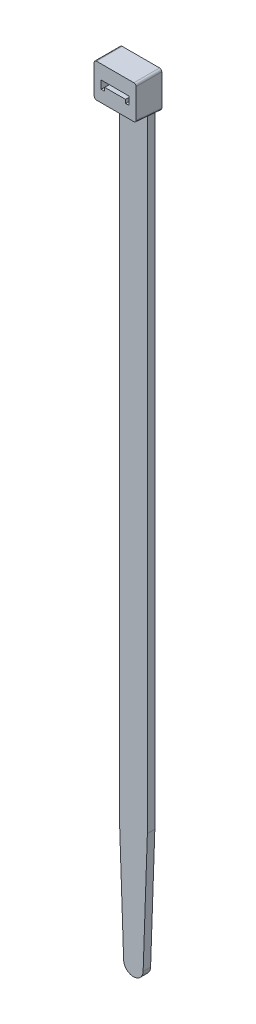
SolidWorks part; units mm, degrees
ref_plane "Front Plane" through (0, 0, 0) normal (0, 0, 1) x (1, 0, 0)
ref_plane "Top Plane" through (0, 0, 0) normal (0, 1, 0) x (1, 0, 0)
ref_plane "Right Plane" through (0, 0, 0) normal (1, 0, 0) x (0, 0, -1)
sketch "Sketch1" plane through (0, 0, 0) normal (0, 0, 1) x (1, 0, 0)
  line L0 (0, 0) -> (0, -49.9735) construction
  line L1 (-22.1748, 6.5086) -> (4.8438, 6.5086) construction
  line L2 (3.81, 0) -> (3.81, -180.234)
  line L3 (-3.81, -180.234) -> (-3.81, 7.4712) construction
  line L4 (3.81, -180.234) -> (2.654, -213.337)
  line L7 (3.81, 0) -> (0, 0)
  line L8 (0, -215.9) -> (0, 0)
  line L9 (0, -9.8) -> (6.4573, -9.8) construction
  arc A0 (2.654, -213.337) -> (0, -215.9) centre (0, -213.2444) cw
  dimension "D1" = 7.62
  dimension "D2" = 9.8
  dimension "D3" = 170.434
  dimension "D4" = 215.9
  dimension "D6" = 2
extrude "Boss-Extrude1" add sketch "Sketch1" along normal blind 2.032
sketch "Sketch5" plane through (0, 0, 0) normal (-1, 0, 0) x (0, 0, 1)
  line L0 (0, 0) -> (7, 0)
  line L1 (7, 0) -> (7, -9.1876)
  line L2 (7, -9.1876) -> (0, -9.8)
  line L4 (0, -9.8) -> (0, 0)
  dimension "D1" = 5
  dimension "D2" = 7
extrude "Boss-Extrude2" add sketch "Sketch5" against normal blind 5.7
sketch "Sketch4" plane through (0, 0, 7) normal (0, 0, 1) x (1, 0, 0)
  line L0 (0, -3.8) -> (3.8, -3.8)
  line L1 (0, -9.6222) -> (0, -215.9) construction
  line L2 (3.8, -3.8) -> (3.8, -6)
  line L3 (3.8, -6) -> (2.85, -6)
  line L4 (2.85, -6) -> (2.85, -5.05)
  line L5 (2.85, -5.05) -> (0, -5.05)
  line L6 (0, -5.05) -> (0, -3.8)
  line L8 (0, 0) -> (0, -9.0011) construction
  line L9 (5.7, 0) -> (0, 0) construction
  dimension "D1" = 3.8
  dimension "D2" = 7.6
  dimension "D3" = 2.2
  dimension "D4" = 1.25
  dimension "D5" = 5.7
extrude "Cut-Extrude1" cut sketch "Sketch4" against normal up to surface (7 mm away) up to face at (3.1703, -89.9439, 0)
fillet "Fillet1" radius 0.6 2 edges at (5.7, -9.4938, 3.5) (5.7, 0, 3.5)
mirror "Mirror1" about plane through (0, -215.9, 2.032) normal (1, 0, 0) of bodies 102
sketch "Sketch6" plane through (0, 0, 0) normal (0, 0, 1) x (1, 0, 0)
  line L1 (5.1307, -4.816) -> (-3.8117, -4.816) construction
  line L3 (3.8, -3.8) -> (-3.8, -3.8) construction
  line L4 (5.1, 0) -> (-5.1, 0) construction
  line L5 (5.1, 0) -> (-5.1, 0) construction
  arc A1 (-2.654, -213.337) -> (2.654, -213.337) centre (0, -213.2444) ccw construction
  dimension "D3" = 215.9
  dimension "D1" = 211.084
  dimension "D2" = 1.016
ref_plane "Plane1" [suppressed] through (0, -9.7256, 0.8509) normal (0, -0.9962, 0.0872) x (-1, 0, 0)
other "SurfaceCut1" [suppressed]
